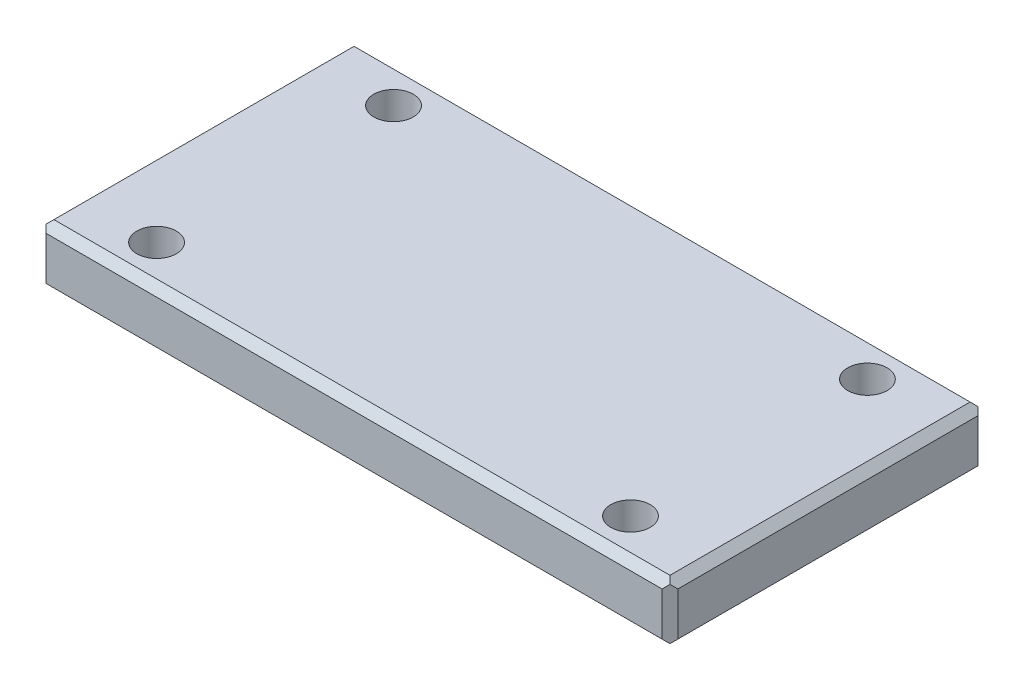
SolidWorks part; units mm, degrees
ref_plane "Front Plane" through (0, 0, 0) normal (0, 0, 1) x (1, 0, 0)
ref_plane "Top Plane" through (0, 0, 0) normal (0, 1, 0) x (1, 0, 0)
ref_plane "Right Plane" through (0, 0, 0) normal (1, 0, 0) x (0, 0, -1)
sketch "Sketch1" plane through (0, 0, 0) normal (0, 1, 0) x (1, 0, 0)
  line L1 (2, 1) -> (-2, 1)
  line L2 (2, 1) -> (2, -1)
  line L3 (2, -1) -> (-2, -1)
  line L4 (-2, 1) -> (-2, -1)
  line L5 (2, 1) -> (-2, -1) construction
  line L6 (2, -1) -> (-2, 1) construction
  line L7 (1.5, -0.75) -> (-1.5, -0.75) construction
  line L8 (1.5, -0.75) -> (1.5, 0.75) construction
  line L9 (1.5, 0.75) -> (-1.5, 0.75) construction
  line L10 (-1.5, -0.75) -> (-1.5, 0.75) construction
  line L11 (1.5, -0.75) -> (-1.5, 0.75) construction
  line L12 (1.5, 0.75) -> (-1.5, -0.75) construction
  circle A0 centre (-1.5, 0.75) radius 0.125
  circle A1 centre (1.5, 0.75) radius 0.125
  circle A2 centre (1.5, -0.75) radius 0.125
  circle A3 centre (-1.5, -0.75) radius 0.125
  point P0 (0, 0)
  point P6 (0, 0)
  dimension "D5" = 0.25
  dimension "D1" = 4
  dimension "D2" = 2
  dimension "D3" = 3
  dimension "D4" = 1.5
extrude "Boss-Extrude1" add sketch "Sketch1" along normal mid plane 0.375
chamfer "Chamfer1" distance 0.05 angle 45 8 edges at (-2, -0.1875, 0) (0, -0.1875, 1) (2, -0.1875, 0) (0, -0.1875, -1) (2, 0.1875, 0) (0, 0.1875, -1) (-2, 0.1875, 0) (0, 0.1875, 1)
chamfer "Chamfer2" distance 0.05 angle 45 4 edges at (2, 0, 1) (2, 0, -1) (-2, 0, 1) (-2, 0, -1)
